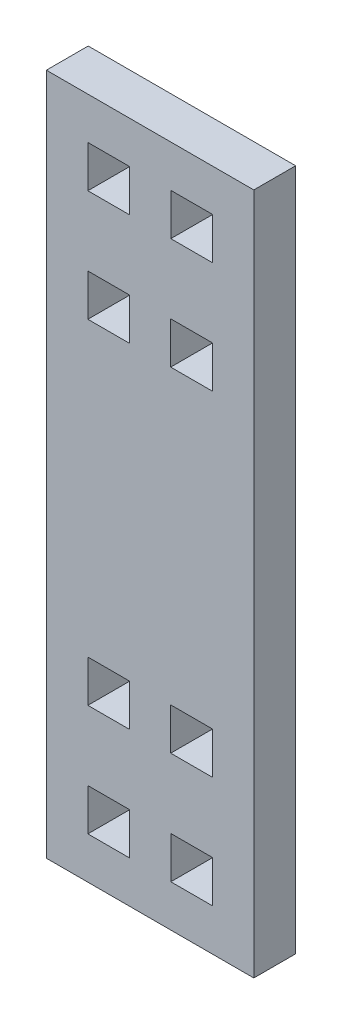
SolidWorks part; units mm, degrees
ref_plane "Front Plane" through (0, 0, 0) normal (0, 0, 1) x (1, 0, 0)
ref_plane "Top Plane" through (0, 0, 0) normal (0, 1, 0) x (1, 0, 0)
ref_plane "Right Plane" through (0, 0, 0) normal (1, 0, 0) x (0, 0, -1)
sketch "Sketch1" plane through (0, 0, 0) normal (0, 0, 1) x (1, 0, 0)
  line L1 (0, 0) -> (25.53, 0)
  line L2 (0, 0) -> (0, 84)
  line L3 (0, 84) -> (25.53, 84)
  line L4 (25.53, 0) -> (25.53, 84)
  dimension "D1" = 84
  dimension "D2" = 25.53
extrude "Boss-Extrude1" add sketch "Sketch1" along normal blind 5.15
sketch "Sketch2" plane through (0, 0, 5.15) normal (0, 0, 1) x (1, 0, 0)
  line L0 (25.53, 42) -> (-8.1809, 42) construction
  line L1 (2.8325, 0) -> (-2.8325, 0) construction
  line L2 (20.424, 69.2185) -> (25.53, 69.2185) construction
  line L3 (5.106, 78.85) -> (10.212, 78.85)
  line L4 (5.106, 78.85) -> (5.106, 73.7)
  line L5 (5.106, 73.7) -> (10.212, 73.7)
  line L6 (10.212, 78.85) -> (10.212, 73.7)
  line L7 (15.318, 78.85) -> (20.424, 78.85)
  line L8 (15.318, 78.85) -> (15.318, 73.7)
  line L9 (15.318, 73.7) -> (20.424, 73.7)
  line L10 (20.424, 78.85) -> (20.424, 73.7)
  line L11 (25.53, 0) -> (25.53, 84) construction
  line L12 (20.4532, 18.85) -> (20.4532, 24)
  line L13 (5.106, 70.4299) -> (0, 70.4299) construction
  line L14 (0, -2.8325) -> (0, 2.8325) construction
  line L15 (25.53, 84) -> (0, 84) construction
  line L16 (5.106, 65.15) -> (10.256, 65.15)
  line L17 (5.106, 65.15) -> (5.106, 60)
  line L18 (5.106, 60) -> (10.256, 60)
  line L19 (10.256, 65.15) -> (10.256, 60)
  line L20 (15.3032, 65.15) -> (20.4532, 65.15)
  line L21 (15.3032, 65.15) -> (15.3032, 60)
  line L22 (15.3032, 60) -> (20.4532, 60)
  line L23 (20.4532, 65.15) -> (20.4532, 60)
  line L24 (15.3032, 24) -> (20.4532, 24)
  line L25 (15.3032, 18.85) -> (15.3032, 24)
  line L26 (15.3032, 18.85) -> (20.4532, 18.85)
  line L27 (10.256, 18.85) -> (10.256, 24)
  line L28 (5.106, 24) -> (10.256, 24)
  line L29 (5.106, 18.85) -> (5.106, 24)
  line L30 (5.106, 18.85) -> (10.256, 18.85)
  line L44 (20.424, 5.15) -> (20.424, 10.3)
  line L45 (15.318, 10.3) -> (20.424, 10.3)
  line L46 (15.318, 5.15) -> (20.424, 5.15)
  line L47 (10.212, 5.15) -> (10.212, 10.3)
  line L48 (5.106, 5.15) -> (10.212, 5.15)
  line L49 (5.106, 5.15) -> (5.106, 10.3)
  line L50 (5.106, 10.3) -> (10.212, 10.3)
  line L51 (15.318, 5.15) -> (15.318, 10.3)
  dimension "D1" = 5.15
  dimension "D2" = 5.15
  dimension "D3" = 5.15
  dimension "D4" = 5.15
  dimension "D5" = 5.15
  dimension "D6" = 18
extrude "Cut-Extrude1" cut sketch "Sketch2" against normal through all
